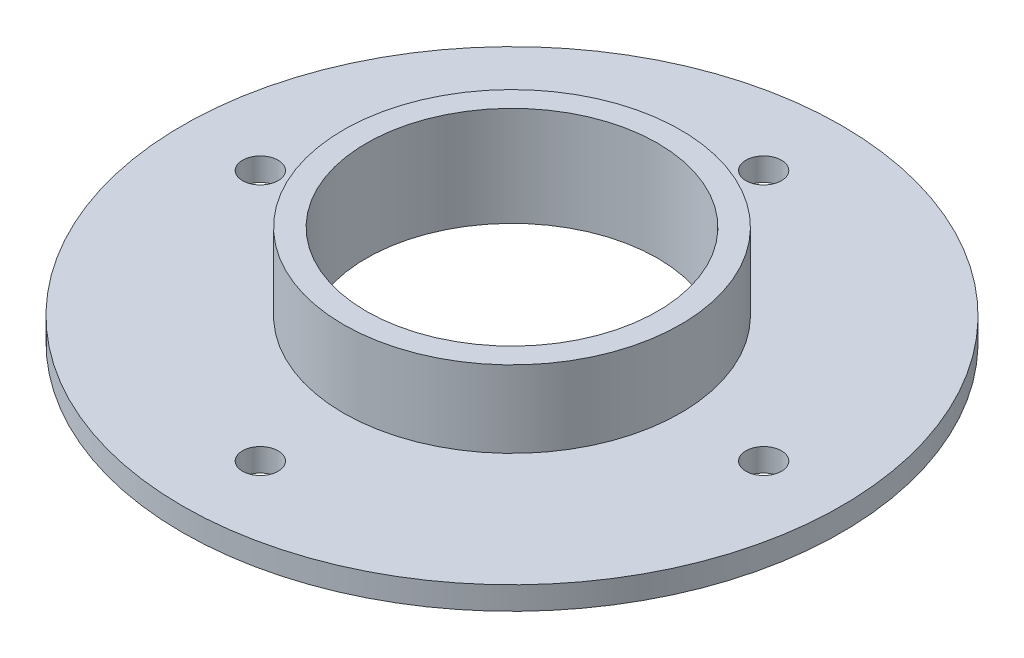
SolidWorks part; units mm, degrees
ref_plane "前视基准面" through (0, 0, 0) normal (0, 0, 1) x (1, 0, 0)
ref_plane "上视基准面" through (0, 0, 0) normal (0, 1, 0) x (1, 0, 0)
ref_plane "右视基准面" through (0, 0, 0) normal (1, 0, 0) x (0, 0, -1)
sketch "草图1" plane through (0, 0, 0) normal (0, 1, 0) x (1, 0, 0)
  circle A0 centre (0, 0) radius 43
  dimension "D1" = 86
extrude "凸台-拉伸1" add sketch "草图1" along normal blind 3
sketch "草图2" plane through (0, 3, 0) normal (0, 1, 0) x (1, 0, 0)
  circle A0 centre (0, 0) radius 22
  circle A1 centre (0, 0) radius 19
  dimension "D1" = 3
  dimension "D2" = 38
extrude "凸台-拉伸2" add sketch "草图2" along normal blind 10
sketch "草图3" plane through (0, 3, 0) normal (0, 1, 0) x (1, 0, 0)
  circle A0 centre (0, 0) radius 19
  circle A1 centre (0, 32.8377) radius 2.3202
  circle A2 centre (32.8377, 0) radius 2.3202
  circle A3 centre (0, -32.8377) radius 2.3202
  circle A4 centre (-32.8377, 0) radius 2.3202
  point P14 (0, 0)
  dimension "D2" = 38
  dimension "D1" = 4
extrude "切除-拉伸1" cut sketch "草图3" against normal blind 20
